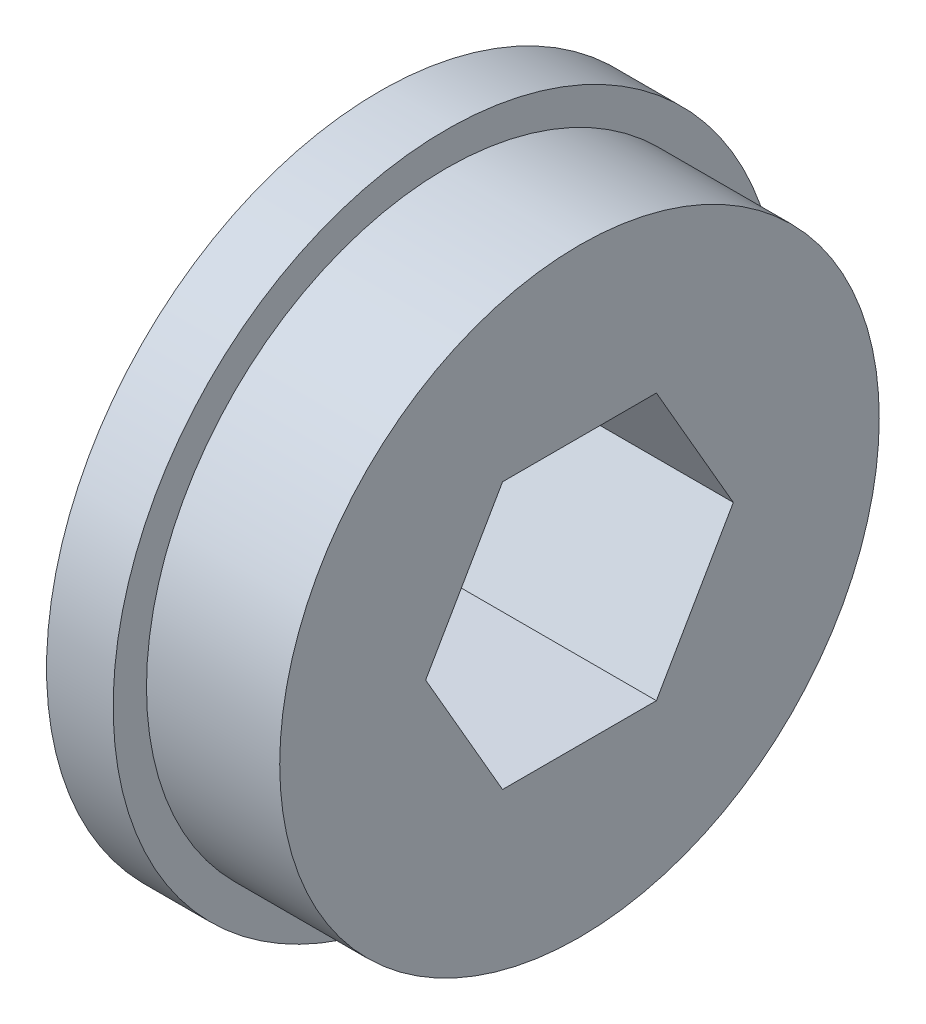
SolidWorks part; units mm, degrees
ref_plane "Front Plane" through (0, 0, 0) normal (0, 0, 1) x (1, 0, 0)
ref_plane "Top Plane" through (0, 0, 0) normal (0, 1, 0) x (1, 0, 0)
ref_plane "Right Plane" through (0, 0, 0) normal (1, 0, 0) x (0, 0, -1)
sketch "Sketch1" plane through (0, 0, 0) normal (1, 0, 0) x (0, 0, -1)
  circle A0 centre (0, 0) radius 15.875
  dimension "D1" = 31.75
extrude "Boss-Extrude1" add sketch "Sketch1" along normal blind 3.175
sketch "Sketch2" plane through (3.175, 0, 0) normal (1, 0, 0) x (0, 0, -1)
  circle A0 centre (0, 0) radius 14.2875
  dimension "D1" = 28.575
extrude "Boss-Extrude2" add sketch "Sketch2" along normal blind 6.35
sketch "Sketch3" plane through (9.525, 0, 0) normal (1, 0, 0) x (0, 0, -1)
  line L1 (7.3323, 0) -> (3.6662, 6.35)
  line L2 (3.6662, 6.35) -> (-3.6662, 6.35)
  line L3 (-3.6662, 6.35) -> (-7.3323, 0)
  line L4 (-7.3323, 0) -> (-3.6662, -6.35)
  line L5 (-3.6662, -6.35) -> (3.6662, -6.35)
  line L6 (3.6662, -6.35) -> (7.3323, 0)
  circle A0 centre (0, 0) radius 6.35 construction
  dimension "D1" = 12.7
extrude "Cut-Extrude1" cut sketch "Sketch3" against normal through all
